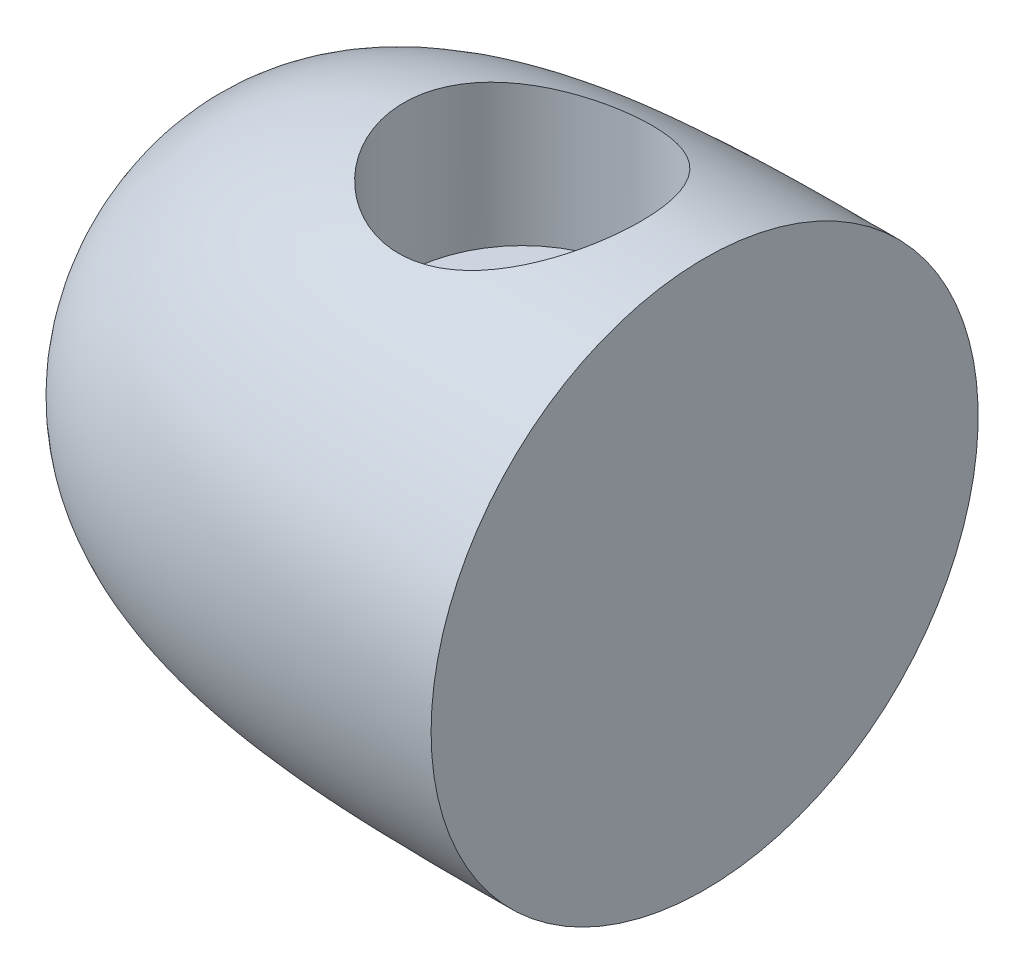
SolidWorks part; units mm, degrees
ref_plane "Front Plane" through (0, 0, 0) normal (0, 0, 1) x (1, 0, 0)
ref_plane "Top Plane" through (0, 0, 0) normal (0, 1, 0) x (1, 0, 0)
ref_plane "Right Plane" through (0, 0, 0) normal (1, 0, 0) x (0, 0, -1)
sketch "Sketch1" plane through (0, 0, 0) normal (0, 0, 1) x (1, 0, 0)
  line L0 (-38.1, 0) -> (0, 0)
  line L1 (0, 0) -> (0, 19.05)
  line L2 (-71.9485, 0) -> (18.6412, 0) construction
  line L3 (-38.1, 0) -> (-38.1, 19.05) construction
  line L4 (-38.1, 19.05) -> (0, 19.05) construction
  spline S0 degree 3 poles (-38.1, 0) (-38.1, 19.5116) (-17.2372, 19.05) (0, 19.05) knots 0 0 0 0 1 1 1 1
  dimension "D1" = 38.1
  dimension "D2" = 38.1
revolve "Revolve1" add sketch "Sketch1" angle 360 about L2
ref_plane "Plane1" through (0, 7.62, 0) normal (0, 1, 0) x (1, 0, 0)
sketch "Sketch3" plane through (0, 7.62, 0) normal (0, 1, 0) x (1, 0, 0)
  line L0 (0, -19.05) -> (0, 19.05) construction
  circle A0 centre (-12.7, 0) radius 8.255
  dimension "D1" = 16.51
  dimension "D2" = 12.7
extrude "Cut-Extrude2" cut sketch "Sketch3" along normal through all
ref_plane "Plane2" through (-37, 0, 0) normal (1, 0, 0) x (0, 0, -1)
sketch "Sketch4" plane through (-37, 0, 0) normal (1, 0, 0) x (0, 0, -1)
  circle A0 centre (0, 0) radius 12.3971
extrude "Cut-Extrude3" cut sketch "Sketch4" against normal blind 10
